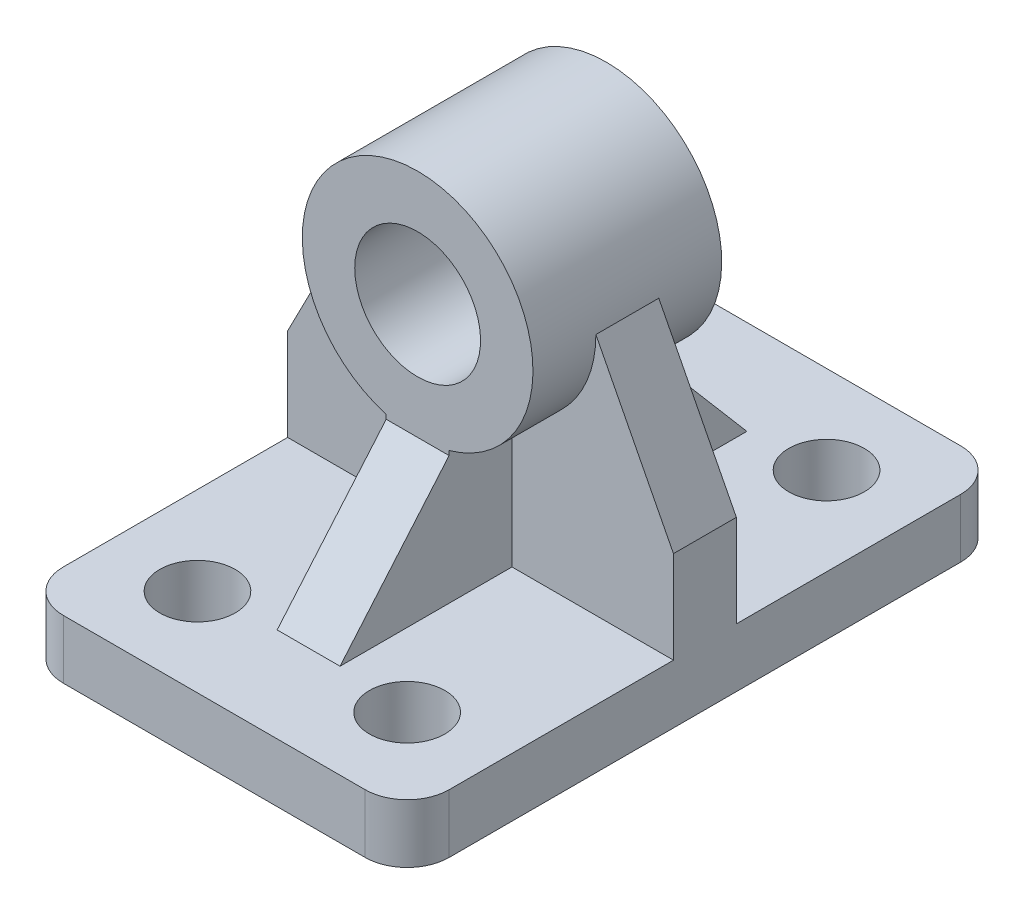
SolidWorks part; units mm, degrees
ref_plane "Alzado" through (0, 0, 0) normal (0, 0, 1) x (1, 0, 0)
ref_plane "Planta" through (0, 0, 0) normal (0, 1, 0) x (1, 0, 0)
ref_plane "Vista lateral" through (0, 0, 0) normal (1, 0, 0) x (0, 0, -1)
sketch "Croquis1" plane through (0, 0, 0) normal (0, 1, 0) x (1, 0, 0)
  line L1 (-111.4014, 85.3605) -> (-19.4014, 85.3605)
  line L2 (-111.4014, 85.3605) -> (-111.4014, -56.6395)
  line L3 (-111.4014, -56.6395) -> (-19.4014, -56.6395)
  line L4 (-19.4014, 85.3605) -> (-19.4014, -56.6395)
  circle A0 centre (-90.4014, 64.3605) radius 9
  circle A1 centre (-90.4014, -35.6395) radius 9
  circle A2 centre (-40.4014, 64.3605) radius 9
  circle A3 centre (-40.4014, -35.6395) radius 9
  dimension "D11" = 18
  dimension "D12" = 18
  dimension "D13" = 18
  dimension "D14" = 18
  dimension "D1" = 142
  dimension "D2" = 92
  dimension "D3" = 21
  dimension "D4" = 21
  dimension "D5" = 21
  dimension "D6" = 21
  dimension "D7" = 21
  dimension "D8" = 21
  dimension "D9" = 21
  dimension "D10" = 21
extrude "Saliente-Extruir1" add sketch "Croquis1" along normal blind 100
sketch "Croquis2" plane through (0, 0, 56.6395) normal (0, 0, 1) x (1, 0, 0)
  line L0 (-92.9014, 72) -> (-111.4014, 36)
  line L1 (-111.4014, 100) -> (-111.4014, 0) construction
  line L2 (-111.4014, 36) -> (-111.4014, 100)
  line L3 (-111.4014, 100) -> (-19.4014, 100)
  line L4 (-19.4014, 100) -> (-19.4014, 36)
  line L5 (-19.4014, 100) -> (-19.4014, 0) construction
  line L6 (-19.4014, 36) -> (-37.9014, 72)
  line L7 (-111.4014, 0) -> (-19.4014, 0) construction
  circle A0 centre (-65.4014, 72) radius 15
  circle A1 centre (-65.4014, 72) radius 27.5
  line M5 (-19.4014, 0) -> (-19.4014, 100)
  line M6 (-19.4014, 100) -> (-111.4014, 100)
  line M7 (-111.4014, 100) -> (-111.4014, 0)
  dimension "D3" = 55
  dimension "D4" = 30
  dimension "D1" = 36
  dimension "D2" = 36
  dimension "D5" = 72
  dimension "D6" = 46
extrude "Cortar-Extruir1" cut sketch "Croquis2" against normal blind 142 contours A1 L6 L0 M5 M6 M7 | A0
sketch "Croquis3" plane through (-19.4014, 0, 0) normal (1, 0, 0) x (0, 0, -1)
  line L0 (14.3605, 102.7907) -> (14.3605, -14.1941) construction
  line L1 (85.3605, 36) -> (85.3605, 0) construction
  line L2 (62.8605, 14) -> (36.8605, 44.5)
  line L3 (-56.6395, 14) -> (-34.1395, 14)
  line L4 (-56.6395, 36) -> (-56.6395, 0) construction
  line L5 (-34.1395, 14) -> (-8.1395, 44.5)
  line L6 (-8.1395, 44.5) -> (-8.1395, 99.5)
  line L7 (85.3605, 99.5) -> (-56.6395, 99.5) construction
  line L8 (-8.1395, 99.5) -> (-56.6395, 99.5)
  line L9 (-56.6395, 99.5) -> (-56.6395, 72) construction
  line L10 (-56.6395, 99.5) -> (-56.6395, 14)
  line L11 (85.3605, 14) -> (62.8605, 14)
  line L12 (85.3605, 99.5) -> (85.3605, 14)
  line L13 (36.8605, 99.5) -> (85.3605, 99.5)
  line L14 (36.8605, 44.5) -> (36.8605, 99.5)
  dimension "D1" = 71
  dimension "D2" = 48.5
  dimension "D3" = 14
  dimension "D4" = 22.5
  dimension "D5" = 55
extrude "Cortar-Extruir2" cut sketch "Croquis3" against normal blind 92
sketch "Croquis4" plane through (0, 0, 56.6395) normal (0, 0, 1) x (1, 0, 0)
  line L0 (-65.4014, 108.2087) -> (-65.4014, -15.1328) construction
  line L1 (-111.4014, 36) -> (-92.9014, 72)
  line L2 (-57.9014, 45.5425) -> (-57.9014, 14)
  line L3 (-111.4014, 14) -> (-19.4014, 14) construction
  line L4 (-111.4014, 14) -> (-111.4014, 36)
  line L5 (-72.9014, 14) -> (-111.4014, 14)
  line L6 (-57.9014, 14) -> (-19.4014, 14)
  line L7 (-19.4014, 14) -> (-19.4014, 36)
  line L8 (-19.4014, 36) -> (-37.9014, 72)
  line L9 (-72.9014, 45.5425) -> (-72.9014, 14)
  circle A0 centre (-65.4014, 72) radius 27.5
  line M8 (-19.4014, 14) -> (-111.4014, 14)
  dimension "D1" = 55
  dimension "D2" = 7.5
extrude "Cortar-Extruir3" cut sketch "Croquis4" against normal blind 63.5 contours A0 L1 L4 L9 M8 | A0 L2 L7 L8 M8
sketch "Croquis7" plane through (0, 0, -85.3605) normal (0, 0, -1) x (-1, 0, 0)
  line L0 (65.4014, 120.3903) -> (65.4014, -7.7797) construction
  line L1 (72.9014, 45.5425) -> (72.9014, 14)
  line L2 (81.5272, 14) -> (49.2755, 14) construction
  line L3 (72.9014, 14) -> (111.4014, 14)
  line L4 (111.4014, 14) -> (111.4014, 36)
  line L5 (111.4014, 36) -> (92.9014, 72)
  line L6 (57.9014, 45.5425) -> (57.9014, 14)
  line L7 (57.9014, 14) -> (19.4014, 14)
  line L8 (19.4014, 14) -> (19.4014, 36)
  line L9 (19.4014, 36) -> (37.9014, 72)
  circle A0 centre (65.4014, 72) radius 27.5
  line M8 (111.4014, 14) -> (19.4014, 14)
  dimension "D1" = 55
  dimension "D2" = 7.5
extrude "Cortar-Extruir4" cut sketch "Croquis7" against normal blind 63.5 contours A0 L9 L8 L6 M8 | A0 L1 L4 L5 M8
fillet "Redondeo1" radius 10 4 edges at (-111.4014, 7, -85.3605) (-19.4014, 7, -85.3605) (-111.4014, 7, 56.6395) (-19.4014, 7, 56.6395)
